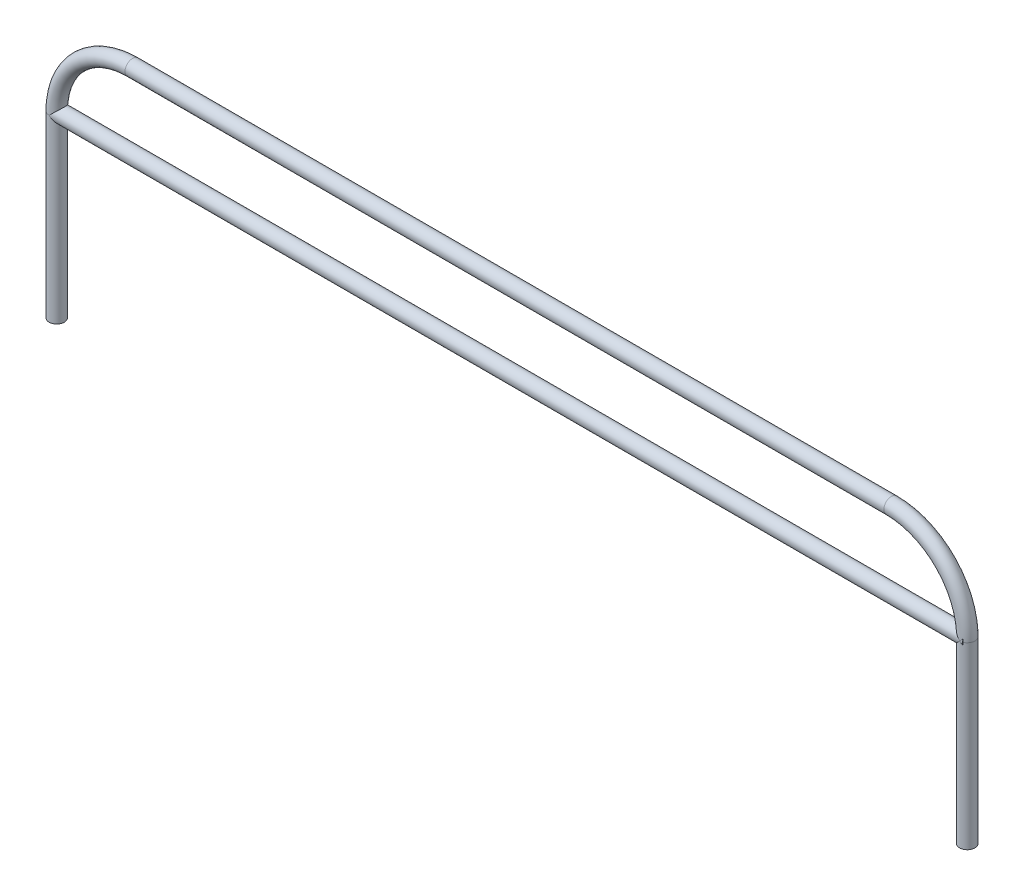
SolidWorks part; units mm, degrees
ref_plane "Front Plane" through (0, 0, 0) normal (0, 0, 1) x (1, 0, 0)
ref_plane "Top Plane" through (0, 0, 0) normal (0, 1, 0) x (1, 0, 0)
ref_plane "Right Plane" through (0, 0, 0) normal (1, 0, 0) x (0, 0, -1)
sketch "Sketch1" plane through (0, 0, 0) normal (0, 0, 1) x (1, 0, 0)
  line L0 (0, 0) -> (0, 300)
  line L1 (1524, 300) -> (1524, 0)
  line L3 (127, 427) -> (1397, 427)
  arc A0 (1397, 427) -> (1524, 300) centre (1397, 300) cw
  arc A1 (0, 300) -> (127, 427) centre (127, 300) cw
  dimension "D1" = 127
  dimension "D2" = 1524
  dimension "D3" = 300
sketch "Sketch2" plane through (0, 0, 0) normal (0, 1, 0) x (1, 0, 0)
  circle A0 centre (0, 0) radius 12.7
  dimension "D1" = 25.4
sweep "Sweep1" add profiles "Sketch2" path "Sketch1"
sketch "Sketch4" plane through (0, 0, 0) normal (1, 0, 0) x (0, 0, -1)
  line L0 (-12.7, 300) -> (12.7, 300) construction
  circle A0 centre (0, 300) radius 12.7
  dimension "D1" = 25.4
extrude "Boss-Extrude2" add sketch "Sketch4" along normal blind 1528.8
